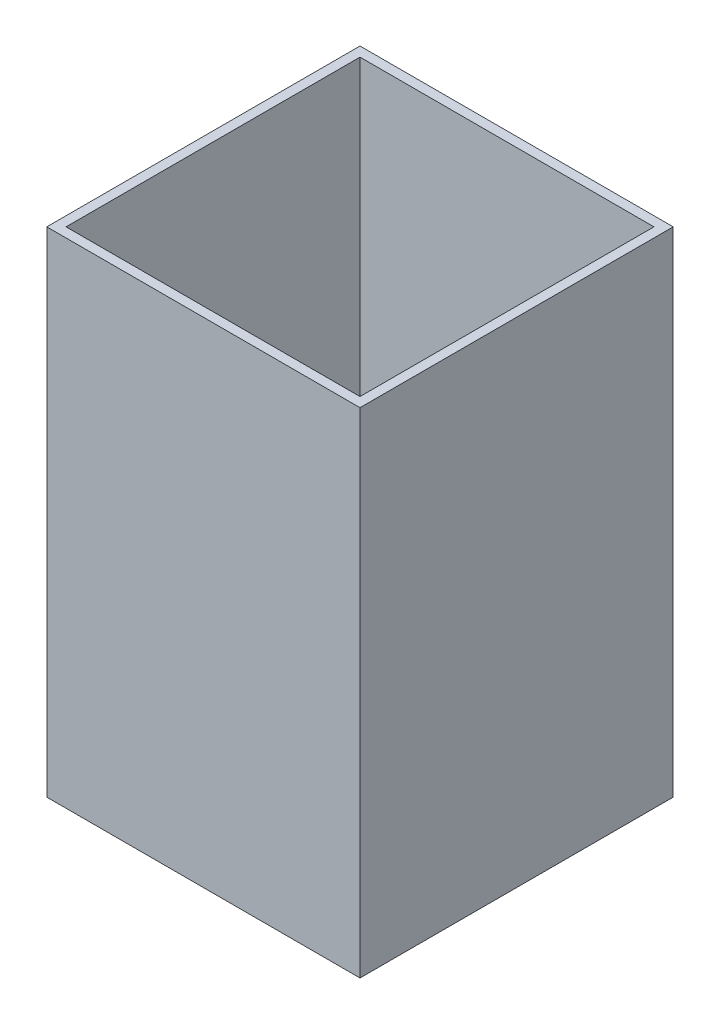
SolidWorks part; units mm, degrees
material "ABS"
ref_plane "Front Plane" through (0, 0, 0) normal (0, 0, 1) x (1, 0, 0)
ref_plane "Top Plane" through (0, 0, 0) normal (0, 1, 0) x (1, 0, 0)
ref_plane "Right Plane" through (0, 0, 0) normal (1, 0, 0) x (0, 0, -1)
sketch "Sketch1" plane through (0, 0, 0) normal (0, 1, 0) x (1, 0, 0)
  line L1 (0, 0) -> (82.55, 0)
  line L2 (0, 0) -> (0, -82.55)
  line L3 (0, -82.55) -> (82.55, -82.55)
  line L4 (82.55, 0) -> (82.55, -82.55)
extrude "Boss-Extrude1" add sketch "Sketch1" along normal blind 130.175
shell "Shell1" thickness 2.54
